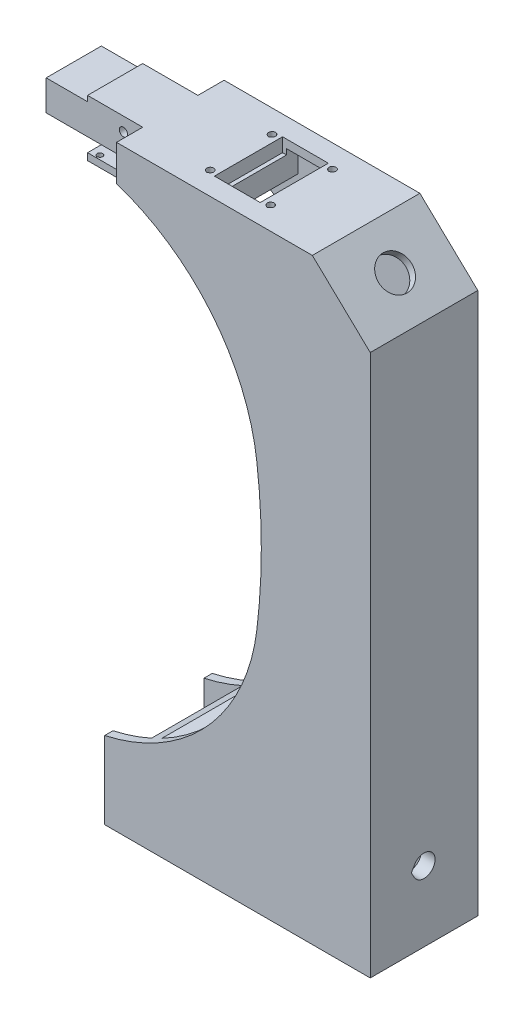
SolidWorks part; units mm, degrees
ref_plane "Спереди" through (0, 0, 0) normal (0, 0, 1) x (1, 0, 0)
ref_plane "Сверху" through (0, 0, 0) normal (0, 1, 0) x (1, 0, 0)
ref_plane "Справа" through (0, 0, 0) normal (1, 0, 0) x (0, 0, -1)
other "Configuration Table"
sketch "Эскиз1" plane through (0, 0, 0) normal (0, 0, 1) x (1, 0, 0)
  line L1 (4.2996, 175.4028) -> (4.2996, 188.4028)
  line L4 (96.2996, 0) -> (96.2996, 168.4028)
  line L7 (75.2996, 188.4028) -> (4.2996, 188.4028)
  line L11 (0, 0) -> (0, -28)
  line L12 (96.2996, 0) -> (96.2996, -28)
  line L13 (96.2996, -28) -> (0, -28)
  line L14 (75.2996, 188.4028) -> (96.2996, 168.4028)
  arc A0 (0, 0) -> (55.1731, 60.6624) centre (-15.2954, 69.3329) ccw
  arc A1 (55.1731, 113.6624) -> (4.2996, 175.4028) centre (-18.7693, 104.5645) ccw
  arc A2 (55.1731, 60.6624) -> (55.1731, 113.6624) centre (-160.2027, 87.1624) ccw
  dimension "D1" = 142
  dimension "D3" = 149
  dimension "D5" = 53
  dimension "D6" = 217
  dimension "D2" = 82
  dimension "D4" = 80
  dimension "D7" = 125.5129
  dimension "D8" = 126.3456
  dimension "D9" = 15.2954
  dimension "D10" = 69.3329
  dimension "D11" = 160.2027
  dimension "D12" = 87.1624
  dimension "D13" = 104.5645
  dimension "D14" = 18.7693
  dimension "D15" = 4.2996
  dimension "D16" = 175.4028
  dimension "D17" = 92
  dimension "D18" = 168.4028
  dimension "D19" = 71
  dimension "D20" = 28
  dimension "D21" = 96.2996
  dimension "D22" = 28
  dimension "D23" = 20
  dimension "D24" = 216.4028
extrude "Бобышка-Вытянуть6" add sketch "Эскиз1" along normal blind 39
sketch "Эскиз5" plane through (0, 0, 0) normal (0, 0, 1) x (1, 0, 0)
  line L3 (34.0996, 175.4028) -> (4.2996, 175.4028)
  line L4 (-18.7004, 169.0219) -> (-18.7004, -25)
  line L8 (34.0996, 175.4028) -> (34.0996, 185.4028)
  line L9 (34.0996, 185.4028) -> (74.0996, 185.4028)
  line L10 (74.0996, 185.4028) -> (91.2996, 169.0219)
  line L11 (96.2996, 168.4028) -> (75.2996, 188.4028) construction
  line L12 (75.2996, 188.4028) -> (4.2996, 188.4028) construction
  line L13 (-18.7004, 169.0219) -> (4.2996, 169.0219)
  line L14 (4.2996, 169.0219) -> (4.2996, 175.4028)
  line L18 (0, -28) -> (96.2996, -28) construction
  line L20 (-18.7004, -25) -> (14, -25)
  line L21 (14, 6.5) -> (14, -25)
  line L22 (91.2996, -25) -> (30.2996, -25)
  line L25 (30.2996, -25) -> (30.2996, 6.5)
  line L27 (14, 6.5) -> (30.2996, 6.5)
  line L28 (91.2996, -25) -> (91.2996, 169.0219)
  line L29 (96.2996, -28) -> (96.2996, 168.4028) construction
  point P9 (0, 0)
  point P15 (0, 0)
  dimension "D2" = 32.7004
  dimension "D3" = 31.5
  dimension "D4" = 3
  dimension "D5" = 3
  dimension "D6" = 40
  dimension "D7" = 23
  dimension "D8" = 5
  dimension "D9" = 6.381
  dimension "D10" = 14
  dimension "D11" = 3
  dimension "D12" = 3
  dimension "D14" = 61
extrude "Вырез-Вытянуть2" cut sketch "Эскиз5" along normal blind 33 from offset 3
sketch "Эскиз7" plane through (0, 0, 0) normal (0, 0, 1) x (1, 0, 0)
  line L1 (4.2996, 188.4028) -> (-30.7004, 188.4028)
  line L2 (4.2996, 188.4028) -> (4.2996, 175.4028)
  line L3 (4.2996, 175.4028) -> (-30.7004, 175.4028)
  line L4 (-30.7004, 188.4028) -> (-30.7004, 175.4028)
  dimension "D1" = 35
extrude "Бобышка-Вытянуть7" add sketch "Эскиз7" along normal blind 20 from offset 9.5
sketch "Эскиз11" plane through (0, 0, 0) normal (0, 0, 1) x (1, 0, 0)
  line L0 (-30.7004, 175.4028) -> (4.2996, 175.4028) construction
  line L1 (6.2996, 175.4028) -> (-10.7004, 175.4028)
  line L2 (6.2996, 175.4028) -> (6.2996, 172.9028)
  line L3 (6.2996, 172.9028) -> (-10.7004, 172.9028)
  line L4 (-10.7004, 175.4028) -> (-10.7004, 172.9028)
  dimension "D2" = 2.5
  dimension "D3" = 17
  dimension "D4" = 15
extrude "Бобышка-Вытянуть15" add sketch "Эскиз11" along normal blind 30 from offset 4.5
sketch "Эскиз12" plane through (0, 0, 0) normal (0, 1, 0) x (1, 0, 0)
  line L1 (-7.7004, -34.1547) -> (-7.2004, -33.866)
  line L2 (-7.7004, -34.1547) -> (-8.2004, -33.866)
  line L4 (-7.7004, -7.1547) -> (-7.2004, -6.866)
  line L5 (-7.7004, -7.1547) -> (-8.2004, -6.866)
  arc A0 (-7.2004, -6.866) -> (-8.2004, -6.866) centre (-7.7004, -6) ccw
  arc A1 (-7.2004, -33.866) -> (-8.2004, -33.866) centre (-7.7004, -33) ccw
  dimension "D1" = 2
  dimension "D2" = 2
  dimension "D3" = 27
  dimension "D4" = 6
  dimension "D5" = 23
  dimension "D6" = 23
  dimension "D7" = 120
  dimension "D8" = 120
  dimension "D9" = 0.5
  dimension "D10" = 0.5
extrude "Вырез-Вытянуть3" cut sketch "Эскиз12" against normal blind 10 from offset 180
sketch "Эскиз13" plane through (0, 0, 0) normal (0, 0, 1) x (1, 0, 0)
  line L0 (4.2996, 188.4028) -> (-30.7004, 188.4028) construction
  line L1 (-30.7004, 188.4028) -> (-30.7004, 175.4028) construction
  circle A0 centre (-2.7004, 183.4028) radius 1.5
  dimension "D1" = 5
  dimension "D3" = 3
  dimension "D2" = 28
extrude "Вырез-Вытянуть4" cut sketch "Эскиз13" along normal blind 30
sketch "Эскиз14" plane through (0, 0, 0) normal (0, 0, 1) x (1, 0, 0)
  line L1 (-30.7004, 188.4028) -> (-15.7004, 188.4028)
  line L2 (-30.7004, 188.4028) -> (-30.7004, 186.4028)
  line L3 (-30.7004, 186.4028) -> (-15.7004, 186.4028)
  line L4 (-15.7004, 188.4028) -> (-15.7004, 186.4028)
  dimension "D1" = 2
  dimension "D2" = 15
extrude "Вырез-Вытянуть5" cut sketch "Эскиз14" along normal blind 30
sketch "Эскиз17" plane through (0, 0, 0) normal (1, 0, 0) x (0, 0, -1)
  line L1 (-24.1188, -2.5) -> (-22.9641, -0.5)
  line L2 (-24.1188, -2.5) -> (-22.9641, -4.5)
  arc A0 (-22.9641, -4.5) -> (-22.9641, -0.5) centre (-19.5, -2.5) ccw
  dimension "D1" = 8
  dimension "D2" = 2.5
  dimension "D3" = 19.5
  dimension "D4" = 120
  dimension "D5" = 2
extrude "Вырез-Вытянуть7" cut sketch "Эскиз17" along normal blind 85 from offset 17
sketch "Эскиз18" plane through (0, 0, 0) normal (1, 0, 0) x (0, 0, -1)
  line L1 (-21.8094, -2.5) -> (-21.2321, -1.5)
  line L2 (-21.8094, -2.5) -> (-21.2321, -3.5)
  arc A0 (-21.2321, -3.5) -> (-21.2321, -1.5) centre (-19.5, -2.5) ccw
  dimension "D1" = 4
  dimension "D2" = 120
  dimension "D3" = 1
extrude "Вырез-Вытянуть9" cut sketch "Эскиз18" along normal blind 5 from offset 13
sketch "Эскиз19" plane through (129.9037, 136.3989, 0) normal (0.6897, 0.7241, 0) x (0, 0, -1)
sketch "Эскиз20" plane through (0, 188.4028, 0) normal (0, 1, 0) x (1, 0, 0)
  line L4 (32.65, -7.15) -> (32.65, -31.85)
  line L5 (32.65, -31.85) -> (49.25, -31.85)
  line L6 (32.65, -7.15) -> (49.25, -7.15)
  line L7 (49.25, -7.15) -> (49.25, -31.85)
  line L9 (30, -32.1434) -> (30.625, -31.7825)
  line L10 (30, -32.1434) -> (29.375, -31.7825)
  line L12 (30, -9.7434) -> (30.625, -9.3825)
  line L13 (30, -9.7434) -> (29.375, -9.3825)
  line L16 (51.9, -9.7434) -> (52.525, -9.3825)
  line L17 (51.9, -9.7434) -> (51.275, -9.3825)
  line L20 (51.9, -32.1434) -> (52.525, -31.7825)
  line L21 (51.9, -32.1434) -> (51.275, -31.7825)
  arc A0 (52.525, -9.3825) -> (51.275, -9.3825) centre (51.9, -8.3) ccw
  arc A1 (52.525, -31.7825) -> (51.275, -31.7825) centre (51.9, -30.7) ccw
  arc A2 (30.625, -9.3825) -> (29.375, -9.3825) centre (30, -8.3) ccw
  arc A3 (30.625, -31.7825) -> (29.375, -31.7825) centre (30, -30.7) ccw
  dimension "D1" = 21.9
  dimension "D13" = 2.5
  dimension "D14" = 2.5
  dimension "D15" = 2.5
  dimension "D16" = 2.5
  dimension "D2" = 22.4
  dimension "D3" = 16.6
  dimension "D4" = 24.7
  dimension "D5" = 30
  dimension "D6" = 21.9
  dimension "D7" = 22.4
  dimension "D8" = 31.3268
  dimension "D9" = 32.65
  dimension "D10" = 7.15
  dimension "D11" = 51.9
  dimension "D12" = 30.7
  dimension "D17" = 49.25
  dimension "D18" = 120
  dimension "D19" = 120
  dimension "D20" = 120
  dimension "D21" = 120
  dimension "D22" = 0.625
  dimension "D23" = 0.625
  dimension "D24" = 0.625
  dimension "D25" = 0.625
extrude "Вырез-Вытянуть10" cut sketch "Эскиз20" against normal blind 5
sketch "Эскиз21" plane through (129.9037, 136.3989, 0) normal (0.6897, 0.7241, 0) x (0, 0, -1)
  line L0 (0, 46.4057) -> (0, 75.4057) construction
  line L1 (0, 60.9057) -> (-39, 60.9057)
  line L2 (-39, 46.4057) -> (-39, 75.4057) construction
  line L3 (-19.5, 75.4057) -> (-19.5, 46.4057)
  line L4 (-39, 75.4057) -> (0, 75.4057) construction
  line L5 (-39, 46.4057) -> (0, 46.4057) construction
  circle A0 centre (-19.5, 60.9057) radius 6
  point P17 (-19.5, 60.9057)
  dimension "D1" = 12
extrude "Вырез-Вытянуть11" cut sketch "Эскиз21" against normal blind 5 contours A0
